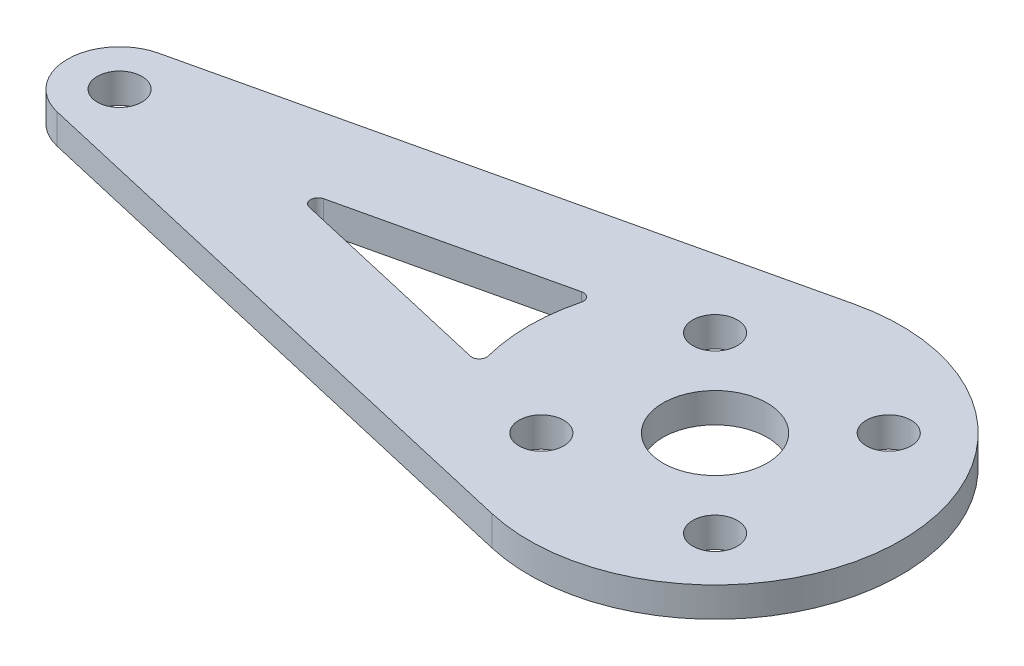
SolidWorks part; units mm, degrees
material "PMMA"
ref_plane "Спереди" through (0, 0, 0) normal (0, 0, 1) x (1, 0, 0)
ref_plane "Сверху" through (0, 0, 0) normal (0, 1, 0) x (1, 0, 0)
ref_plane "Справа" through (0, 0, 0) normal (1, 0, 0) x (0, 0, -1)
sketch "Эскиз1" plane through (0, 0, 0) normal (0, 1, 0) x (1, 0, 0)
  line L0 (0, 0) -> (-40, 0) construction
  line L1 (-40.7875, 3.4103) -> (-2.8125, 12.1795)
  line L2 (-40.7875, -3.4103) -> (-2.8125, -12.1795)
  line L3 (0, 0) -> (5.8336, 5.8336) construction
  line L9 (-28.8889, 0) -> (-11.8658, -3.931)
  line L11 (-28.8889, 0) -> (-11.8658, 3.931)
  circle A0 centre (0, 0) radius 12.5
  circle A1 centre (-40, 0) radius 1.5
  circle A2 centre (-40, 0) radius 3.5
  circle A3 centre (0, 0) radius 3.5
  circle A4 centre (0, 0) radius 8.25 construction
  circle A5 centre (5.8336, 5.8336) radius 1.5
  circle A6 centre (5.8336, -5.8336) radius 1.5
  circle A7 centre (-5.8336, -5.8336) radius 1.5
  circle A8 centre (-5.8336, 5.8336) radius 1.5
  point P14 (-39.4375, -2.4359)
  point P15 (-1.4625, 6.3333)
  point P16 (-39.4375, 2.4359)
  point P23 (0, 0)
  point P24 (-1.4625, -6.3333)
  dimension "D1" = 25
  dimension "D3" = 3
  dimension "D4" = 7
  dimension "D5" = 7
  dimension "D6" = 16.5
  dimension "D7" = 4
  dimension "D2" = 40
extrude "Бобышка-Вытянуть1" add sketch "Эскиз1" along normal blind 2 contours A2 L2 A0 L9 L11 L1 | A0 A8 A7 A6 A5 A3 | A2 A1
fillet "Скругление1" radius 0.5 3 edges at (-28.8889, 1, 0) (-11.8658, 1, -3.931) (-11.8658, 1, 3.931)
